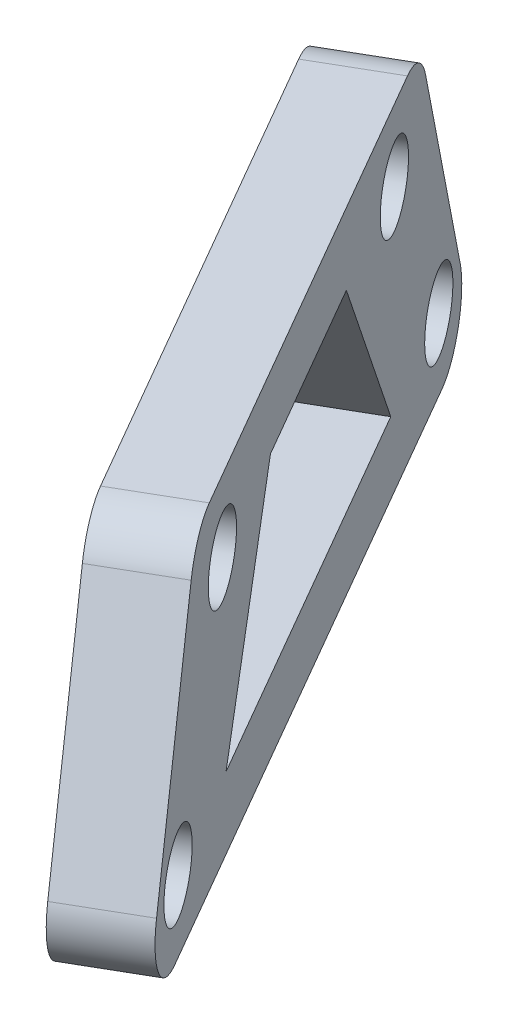
SolidWorks part; units mm, degrees
ref_plane "Front Plane" through (0, 0, 0) normal (0, 0, 1) x (1, 0, 0)
ref_plane "Top Plane" through (0, 0, 0) normal (0, 1, 0) x (1, 0, 0)
ref_plane "Right Plane" through (0, 0, 0) normal (1, 0, 0) x (0, 0, -1)
sketch "Sketch1" plane through (-13.1955, 0, 7.6184) normal (-0.866, 0, 0.5) x (0.5, 0, 0.866)
  line L0 (-25.1342, 118.0559) -> (-17.3608, 136.7988)
  line L1 (-17.3608, 136.7988) -> (16.8858, 136.7988)
  line L2 (16.8858, 136.7988) -> (24.6592, 118.0559)
  line L3 (24.6592, 118.0559) -> (-25.1342, 118.0559)
  line L4 (-13.3608, 132.7988) -> (12.8858, 132.7988) construction
  line L5 (-12.8047, 122.0559) -> (-6.0314, 132.7988)
  line L6 (-17.6728, 114.3347) -> (-12.1063, 123.1637) construction
  line L7 (-10.8995, 125.0777) -> (-5.333, 133.9066) construction
  line L8 (-6.0314, 132.7988) -> (5.5564, 132.7988)
  line L9 (10.4245, 125.0777) -> (4.858, 133.9066) construction
  line L10 (5.5564, 132.7988) -> (12.3297, 122.0559)
  line L11 (17.1978, 114.3347) -> (11.6313, 123.1637) construction
  line L12 (12.3297, 122.0559) -> (-12.8047, 122.0559)
  circle A0 centre (-13.3608, 132.7988) radius 2.15
  circle A1 centre (12.8858, 132.7988) radius 2.15
  circle A2 centre (19.6592, 122.0559) radius 2.15
  circle A3 centre (-20.1342, 122.0559) radius 2.15
  point P0 (-20.1342, 122.0559)
  point P2 (19.6592, 122.0559)
  point P4 (12.8858, 132.7988)
  point P6 (-13.3608, 132.7988)
  point P20 (-0.2375, 136.7988)
  point P21 (-0.2375, 132.7988)
  dimension "D1" = 4.3
  dimension "D2" = 4
  dimension "D3" = 4
  dimension "D4" = 5
  dimension "D5" = 4
  dimension "D6" = 5
  dimension "D7" = 4
  dimension "D8" = 4
extrude "Boss-Extrude1" add sketch "Sketch1" against normal blind 4.45
fillet "Fillet1" radius 3 4 edges at (1.061, 118.0559, 27.8614) (-2.8257, 136.7988, 21.1295) (-19.949, 136.7988, -8.529) (-23.8357, 118.0559, -15.2609)
